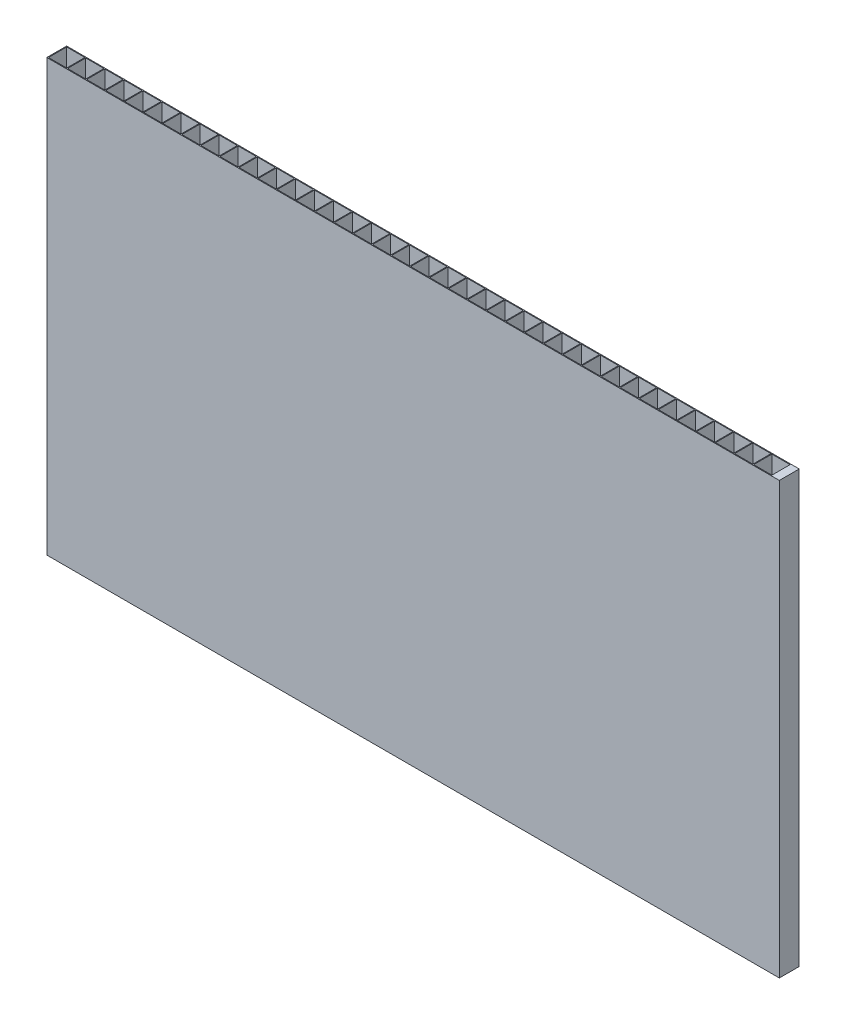
SolidWorks part; units mm, degrees
material "Perspex (TM) GS Acrylic Cast Sheet"
ref_plane "Front Plane" through (0, 0, 0) normal (0, 0, 1) x (1, 0, 0)
ref_plane "Top Plane" through (0, 0, 0) normal (0, 1, 0) x (1, 0, 0)
ref_plane "Right Plane" through (0, 0, 0) normal (1, 0, 0) x (0, 0, -1)
sketch "Sketch1" plane through (0, 0, 0) normal (0, 1, 0) x (1, 0, 0)
  line L0 (6, 5.75) -> (6, 0.25)
  line L1 (0, 0) -> (221, 0)
  line L2 (0, 0) -> (0, 6)
  line L3 (0, 6) -> (221, 6)
  line L4 (221, 0) -> (221, 6)
  line L5 (0.25, 5.75) -> (5.75, 5.75)
  line L6 (0.25, 5.75) -> (0.25, 0.25)
  line L7 (0.25, 0.25) -> (5.75, 0.25)
  line L8 (5.75, 5.75) -> (5.75, 0.25)
  line L9 (6, 5.75) -> (11.5, 5.75)
  line L10 (11.5, 5.75) -> (11.5, 0.25)
  line L11 (6, 0.25) -> (11.5, 0.25)
  line L12 (11.75, 5.75) -> (11.75, 0.25)
  line L13 (11.75, 5.75) -> (17.25, 5.75)
  line L14 (17.25, 5.75) -> (17.25, 0.25)
  line L15 (11.75, 0.25) -> (17.25, 0.25)
  line L16 (17.5, 5.75) -> (17.5, 0.25)
  line L17 (17.5, 5.75) -> (23, 5.75)
  line L18 (23, 5.75) -> (23, 0.25)
  line L19 (17.5, 0.25) -> (23, 0.25)
  line L20 (23.25, 5.75) -> (23.25, 0.25)
  line L21 (23.25, 5.75) -> (28.75, 5.75)
  line L22 (28.75, 5.75) -> (28.75, 0.25)
  line L23 (23.25, 0.25) -> (28.75, 0.25)
  line L24 (29, 5.75) -> (29, 0.25)
  line L25 (29, 5.75) -> (34.5, 5.75)
  line L26 (34.5, 5.75) -> (34.5, 0.25)
  line L27 (29, 0.25) -> (34.5, 0.25)
  line L28 (34.75, 5.75) -> (34.75, 0.25)
  line L29 (34.75, 5.75) -> (40.25, 5.75)
  line L30 (40.25, 5.75) -> (40.25, 0.25)
  line L31 (34.75, 0.25) -> (40.25, 0.25)
  line L32 (40.5, 5.75) -> (40.5, 0.25)
  line L33 (40.5, 5.75) -> (46, 5.75)
  line L34 (46, 5.75) -> (46, 0.25)
  line L35 (40.5, 0.25) -> (46, 0.25)
  line L36 (46.25, 5.75) -> (46.25, 0.25)
  line L37 (46.25, 5.75) -> (51.75, 5.75)
  line L38 (51.75, 5.75) -> (51.75, 0.25)
  line L39 (46.25, 0.25) -> (51.75, 0.25)
  line L40 (52, 5.75) -> (52, 0.25)
  line L41 (52, 5.75) -> (57.5, 5.75)
  line L42 (57.5, 5.75) -> (57.5, 0.25)
  line L43 (52, 0.25) -> (57.5, 0.25)
  line L44 (57.75, 5.75) -> (57.75, 0.25)
  line L45 (57.75, 5.75) -> (63.25, 5.75)
  line L46 (63.25, 5.75) -> (63.25, 0.25)
  line L47 (57.75, 0.25) -> (63.25, 0.25)
  line L48 (63.5, 5.75) -> (63.5, 0.25)
  line L49 (63.5, 5.75) -> (69, 5.75)
  line L50 (69, 5.75) -> (69, 0.25)
  line L51 (63.5, 0.25) -> (69, 0.25)
  line L52 (69.25, 5.75) -> (69.25, 0.25)
  line L53 (69.25, 5.75) -> (74.75, 5.75)
  line L54 (74.75, 5.75) -> (74.75, 0.25)
  line L55 (69.25, 0.25) -> (74.75, 0.25)
  line L56 (75, 5.75) -> (75, 0.25)
  line L57 (75, 5.75) -> (80.5, 5.75)
  line L58 (80.5, 5.75) -> (80.5, 0.25)
  line L59 (75, 0.25) -> (80.5, 0.25)
  line L60 (80.75, 5.75) -> (80.75, 0.25)
  line L61 (80.75, 5.75) -> (86.25, 5.75)
  line L62 (86.25, 5.75) -> (86.25, 0.25)
  line L63 (80.75, 0.25) -> (86.25, 0.25)
  line L64 (86.5, 5.75) -> (86.5, 0.25)
  line L65 (86.5, 5.75) -> (92, 5.75)
  line L66 (92, 5.75) -> (92, 0.25)
  line L67 (86.5, 0.25) -> (92, 0.25)
  line L68 (92.25, 5.75) -> (92.25, 0.25)
  line L69 (92.25, 5.75) -> (97.75, 5.75)
  line L70 (97.75, 5.75) -> (97.75, 0.25)
  line L71 (92.25, 0.25) -> (97.75, 0.25)
  line L72 (98, 5.75) -> (98, 0.25)
  line L73 (98, 5.75) -> (103.5, 5.75)
  line L74 (103.5, 5.75) -> (103.5, 0.25)
  line L75 (98, 0.25) -> (103.5, 0.25)
  line L76 (103.75, 5.75) -> (103.75, 0.25)
  line L77 (103.75, 5.75) -> (109.25, 5.75)
  line L78 (109.25, 5.75) -> (109.25, 0.25)
  line L79 (103.75, 0.25) -> (109.25, 0.25)
  line L80 (109.5, 5.75) -> (109.5, 0.25)
  line L81 (109.5, 5.75) -> (115, 5.75)
  line L82 (115, 5.75) -> (115, 0.25)
  line L83 (109.5, 0.25) -> (115, 0.25)
  line L84 (115.25, 5.75) -> (115.25, 0.25)
  line L85 (115.25, 5.75) -> (120.75, 5.75)
  line L86 (120.75, 5.75) -> (120.75, 0.25)
  line L87 (115.25, 0.25) -> (120.75, 0.25)
  line L88 (121, 5.75) -> (121, 0.25)
  line L89 (121, 5.75) -> (126.5, 5.75)
  line L90 (126.5, 5.75) -> (126.5, 0.25)
  line L91 (121, 0.25) -> (126.5, 0.25)
  line L92 (126.75, 5.75) -> (126.75, 0.25)
  line L93 (126.75, 5.75) -> (132.25, 5.75)
  line L94 (132.25, 5.75) -> (132.25, 0.25)
  line L95 (126.75, 0.25) -> (132.25, 0.25)
  line L96 (132.5, 5.75) -> (132.5, 0.25)
  line L97 (132.5, 5.75) -> (138, 5.75)
  line L98 (138, 5.75) -> (138, 0.25)
  line L99 (132.5, 0.25) -> (138, 0.25)
  line L100 (138.25, 5.75) -> (138.25, 0.25)
  line L101 (138.25, 5.75) -> (143.75, 5.75)
  line L102 (143.75, 5.75) -> (143.75, 0.25)
  line L103 (138.25, 0.25) -> (143.75, 0.25)
  line L104 (144, 5.75) -> (144, 0.25)
  line L105 (144, 5.75) -> (149.5, 5.75)
  line L106 (149.5, 5.75) -> (149.5, 0.25)
  line L107 (144, 0.25) -> (149.5, 0.25)
  line L108 (149.75, 5.75) -> (149.75, 0.25)
  line L109 (149.75, 5.75) -> (155.25, 5.75)
  line L110 (155.25, 5.75) -> (155.25, 0.25)
  line L111 (149.75, 0.25) -> (155.25, 0.25)
  line L112 (155.5, 5.75) -> (155.5, 0.25)
  line L113 (155.5, 5.75) -> (161, 5.75)
  line L114 (161, 5.75) -> (161, 0.25)
  line L115 (155.5, 0.25) -> (161, 0.25)
  line L116 (161.25, 5.75) -> (161.25, 0.25)
  line L117 (161.25, 5.75) -> (166.75, 5.75)
  line L118 (166.75, 5.75) -> (166.75, 0.25)
  line L119 (161.25, 0.25) -> (166.75, 0.25)
  line L120 (167, 5.75) -> (167, 0.25)
  line L121 (167, 5.75) -> (172.5, 5.75)
  line L122 (172.5, 5.75) -> (172.5, 0.25)
  line L123 (167, 0.25) -> (172.5, 0.25)
  line L124 (172.75, 5.75) -> (172.75, 0.25)
  line L125 (172.75, 5.75) -> (178.25, 5.75)
  line L126 (178.25, 5.75) -> (178.25, 0.25)
  line L127 (172.75, 0.25) -> (178.25, 0.25)
  line L128 (178.5, 5.75) -> (178.5, 0.25)
  line L129 (178.5, 5.75) -> (184, 5.75)
  line L130 (184, 5.75) -> (184, 0.25)
  line L131 (178.5, 0.25) -> (184, 0.25)
  line L132 (184.25, 5.75) -> (184.25, 0.25)
  line L133 (184.25, 5.75) -> (189.75, 5.75)
  line L134 (189.75, 5.75) -> (189.75, 0.25)
  line L135 (184.25, 0.25) -> (189.75, 0.25)
  line L136 (190, 5.75) -> (190, 0.25)
  line L137 (190, 5.75) -> (195.5, 5.75)
  line L138 (195.5, 5.75) -> (195.5, 0.25)
  line L139 (190, 0.25) -> (195.5, 0.25)
  line L140 (195.75, 5.75) -> (195.75, 0.25)
  line L141 (195.75, 5.75) -> (201.25, 5.75)
  line L142 (201.25, 5.75) -> (201.25, 0.25)
  line L143 (195.75, 0.25) -> (201.25, 0.25)
  line L144 (201.5, 5.75) -> (201.5, 0.25)
  line L145 (201.5, 5.75) -> (207, 5.75)
  line L146 (207, 5.75) -> (207, 0.25)
  line L147 (201.5, 0.25) -> (207, 0.25)
  line L148 (207.25, 5.75) -> (207.25, 0.25)
  line L149 (207.25, 5.75) -> (212.75, 5.75)
  line L150 (212.75, 5.75) -> (212.75, 0.25)
  line L151 (207.25, 0.25) -> (212.75, 0.25)
  line L152 (213, 5.75) -> (213, 0.25)
  line L153 (213, 5.75) -> (218.5, 5.75)
  line L154 (218.5, 5.75) -> (218.5, 0.25)
  line L155 (213, 0.25) -> (218.5, 0.25)
  line L160 (218.75, 5.75) -> (218.75, 0.25) [skipped]
  line L161 (218.75, 0.25) -> (224.25, 0.25) [skipped]
  line L162 (224.25, 5.75) -> (224.25, 0.25) [skipped]
  line L163 (218.75, 5.75) -> (224.25, 5.75) [skipped]
  point P9 (0.25, 3)
  point P10 (0, 3)
  dimension "D1" = 221
  dimension "D2" = 6
  dimension "D3" = 5.5
  dimension "D4" = 5.5
  dimension "D5" = 0.25
  dimension "D6" = 39
extrude "Boss-Extrude1" add sketch "Sketch1" along normal blind 130 contours L1 L4 L3 L2 | L8 L7 L6 L5 | L0 L11 L10 L9 | L12 L15 L14 L13 | L16 L19 L18 L17 | L20 L23 L22 L21 | L26 L27 L24 L25 | L28 L31 L30 L29 | L32 L35 L34 L33 | L38 L39 L36 L37 | L40 L43 L42 L41 | L46 L47 L44 L45 | L50 L51 L48 L49 | L52 L55 L54 L53 | L56 L59 L58 L57 | L60 L63 L62 L61 | L67 L66 L65 L64 | L71 L70 L69 L68 | L75 L74 L73 L72 | L79 L78 L77 L76 | L83 L82 L81 L80 | L87 L86 L85 L84 | L91 L90 L89 L88 | L94 L95 L92 L93 | L96 L99 L98 L97 | L100 L103 L102 L101 | L104 L107 L106 L105 | L108 L111 L110 L109 | L112 L115 L114 L113 | L116 L119 L118 L117 | L122 L123 L120 L121 | L124 L127 L126 L125 | L128 L131 L130 L129 | L132 L135 L134 L133 | L136 L139 L138 L137 | L140 L143 L142 L141 | L144 L147 L146 L145 | L148 L151 L150 L149 | L152 L155 L154 L153
